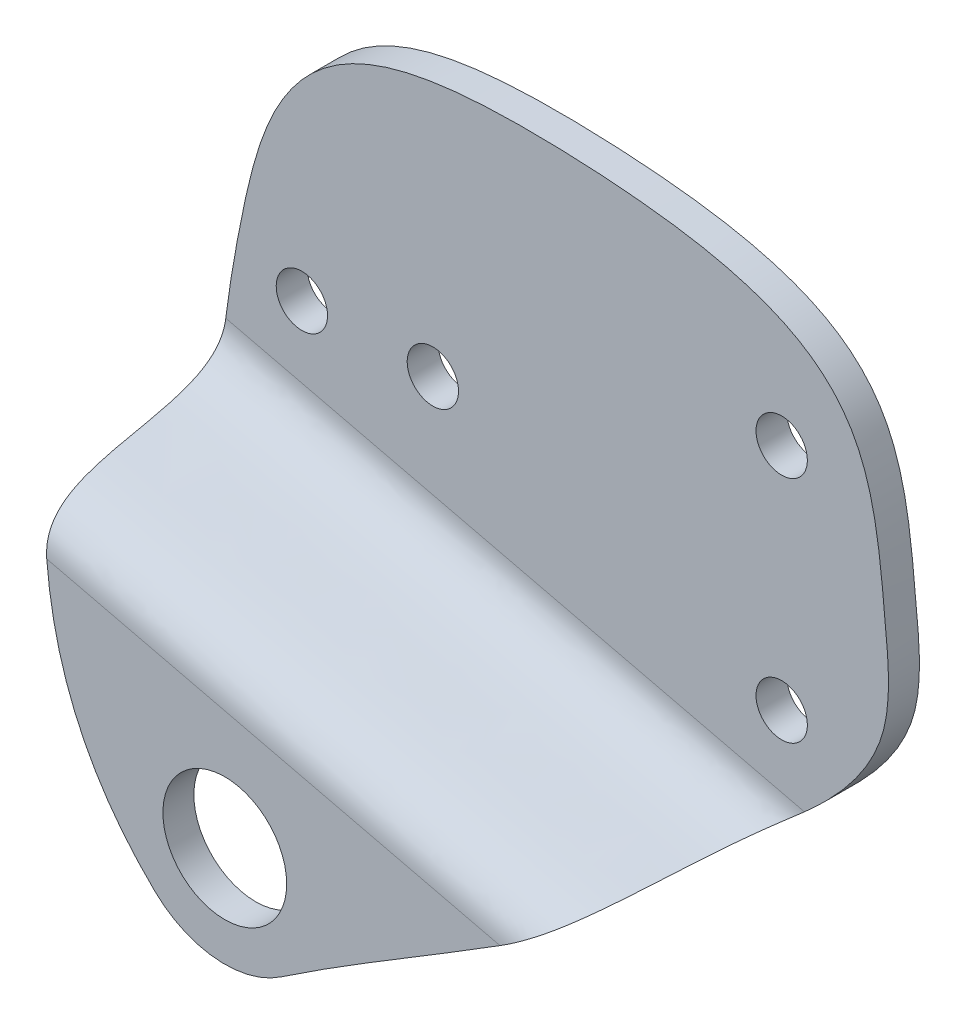
SolidWorks part; units mm, degrees
material "ABS"
ref_plane "Front Plane" through (0, 0, 0) normal (0, 0, 1) x (1, 0, 0)
ref_plane "Top Plane" through (0, 0, 0) normal (0, 1, 0) x (1, 0, 0)
ref_plane "Right Plane" through (0, 0, 0) normal (1, 0, 0) x (0, 0, -1)
sketch "main_features_sketch" plane through (0, 0, 0) normal (0, 0, 1) x (1, 0, 0)
  line L0 (0, -7.3) -> (0, 0) construction
  line L1 (-127, -19.05) -> (127, -19.05) construction
  line L2 (-12.0493, -9.2395) -> (15.4719, -35.7057) construction
  line L3 (-1.2057, -19.8915) -> (-35.1292, -42.8629) construction
  circle A0 centre (-9.525, 25.4) radius 6 construction
  circle A1 centre (3.175, 25.4) radius 6 construction
  circle A2 centre (37, 36.5125) radius 6 construction
  circle A3 centre (37, 14.2875) radius 6 construction
  circle A4 centre (0, -7.3) radius 6
  circle A5 centre (0, -7.3) radius 9.75
  circle A6 centre (-9.525, 25.4) radius 2.4892
  circle A7 centre (3.175, 25.4) radius 2.4892
  circle A8 centre (37, 36.5125) radius 2.4892
  circle A9 centre (37, 14.2875) radius 2.4892
  spline S0 degree 3 poles (-6.7583, -14.3277) (-19.8154, -1.7711) (-17.8681, 18.3746) (-11.5594, 47.1139) (0.7713, 51.6537) (45.1342, 49.0484) (46.0113, 37.2911) (48.8462, 7.8731) (21.9825, -4.1895) (5.4668, -15.3732) knots 0 0 0 0 0.179468 0.221834 0.401236 0.45577 0.712637 0.770271 1 1 1 1
  dimension "D1" = 12
  dimension "D2" = 19.5
  dimension "D4" = 12
  dimension "D5" = 4.9784
  dimension "D3" = 2
extrude "Boss-Extrude1" add sketch "main_features_sketch" along normal blind 20 contours S0 A5 A9 A8 A7 A6 | A5 A4
ref_plane "Plane1" through (4.647, 19.4558, 0) normal (0.2323, 0.9726, 0) x (0.9726, -0.2323, 0)
ref_plane "cut_plane" through (-12.3292, 2.9448, 0) normal (-0.9726, 0.2323, 0) x (0, 0, 1)
sketch "Sketch2" plane through (-12.676, 1.4928, 0) normal (0.9726, -0.2323, 0) x (0, 0, -1)
  line L0 (-3, 56.3464) -> (-3, 17.2679)
  line L1 (-20, -15.3574) -> (-20, 5.6129)
  line L3 (0, -14.0129) -> (0, 56.3464) construction
  line L4 (-20, 2.5676) -> (-20, 15.7103) construction
  line L5 (-3, 22.2829) -> (-3, 34.5715) construction
  line L6 (0, 56.3464) -> (0, 15.4609)
  line L7 (-17, 4.54) -> (-17, -15.3574)
  line L8 (-20, -15.3574) -> (0, -15.3574) construction
  line L9 (0, 56.3464) -> (-20, 56.3464) construction
  line L10 (-3, 56.3464) -> (0, 56.3464)
  line L11 (-17, -15.3574) -> (-20, -15.3574)
  line L12 (-17, 0.1846) -> (-17, 6.182) construction
  line L13 (0, 2.2857) -> (0, 6.7648) construction
  line L14 (0, 15.4609) -> (0, -15.3574)
  line L15 (0, -15.3574) -> (-17, -15.3574)
  line L16 (-20, 5.6129) -> (-20, 56.3464)
  line L17 (-20, 56.3464) -> (-3, 56.3464)
  spline S0 degree 3 poles (-3, 17.2679) (-3, 9.5875) (-20, 13.8271) (-20, 5.6129) knots 0 0 0 0 1 1 1 1
  spline S1 degree 3 poles (0, 15.4609) (0, 9.0167) (-17, 7.0389) (-17, 4.54) knots 0 0 0 0 1 1 1 1
  dimension "D2" = 3
extrude "Cut-Extrude1" cut sketch "Sketch2" against normal through all both and the other way through all contours L0 S0 L16 L17 | S1 L14 L15 L7
